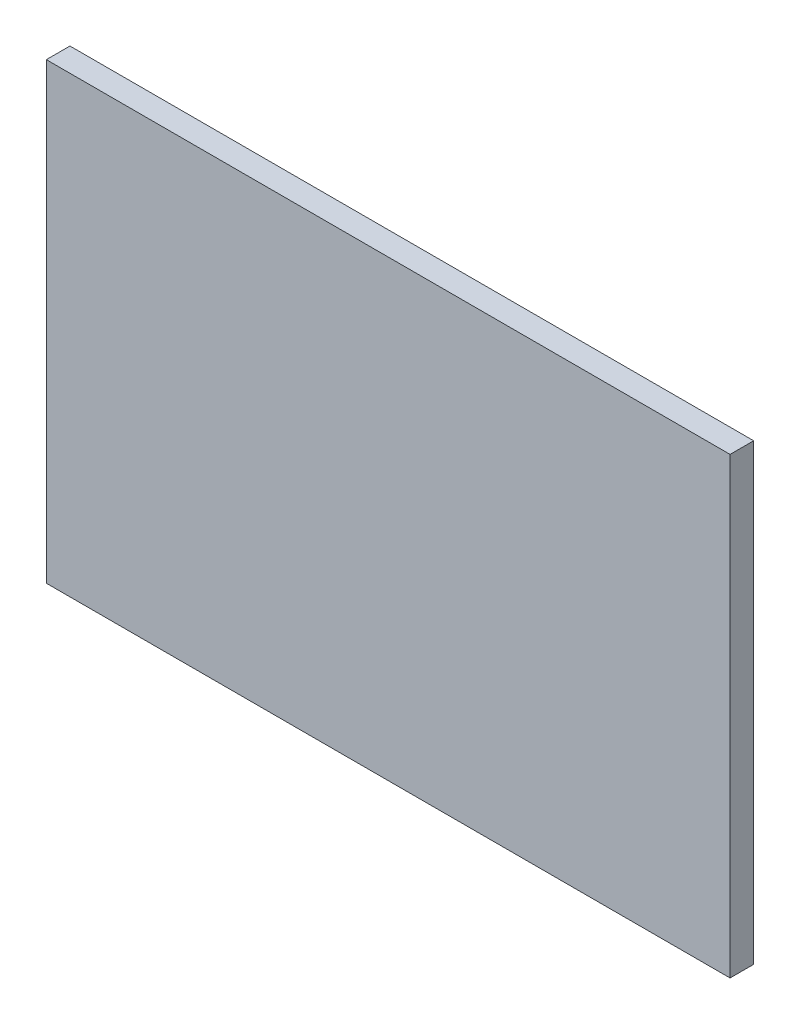
SolidWorks part; units mm, degrees
ref_plane "Front Plane" through (0, 0, 0) normal (0, 0, 1) x (1, 0, 0)
ref_plane "Top Plane" through (0, 0, 0) normal (0, 1, 0) x (1, 0, 0)
ref_plane "Right Plane" through (0, 0, 0) normal (1, 0, 0) x (0, 0, -1)
sketch "Sketch1" plane through (0, 0, 0) normal (0, 1, 0) x (1, 0, 0)
  line L1 (919.1625, -31.75) -> (-919.1625, -31.75)
  line L2 (919.1625, -31.75) -> (919.1625, 31.75)
  line L3 (919.1625, 31.75) -> (-919.1625, 31.75)
  line L4 (-919.1625, -31.75) -> (-919.1625, 31.75)
  line L5 (919.1625, -31.75) -> (-919.1625, 31.75) construction
  line L6 (919.1625, 31.75) -> (-919.1625, -31.75) construction
  point P0 (0, 0)
  dimension "D1" = 63.5
  dimension "D2" = 1838.325
extrude "Boss-Extrude1" add sketch "Sketch1" along normal blind 1219.2
